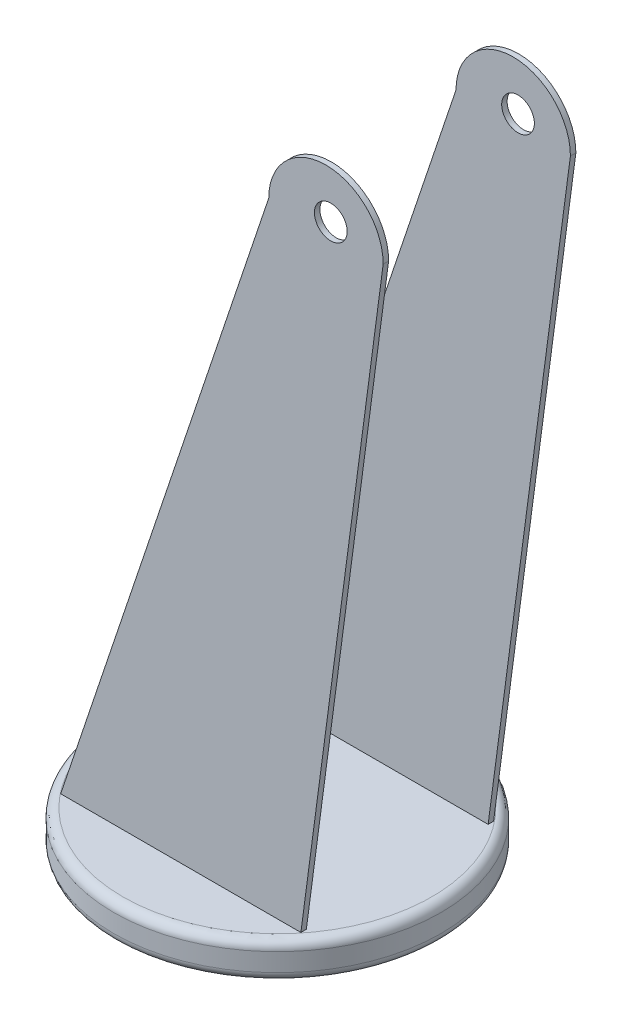
SolidWorks part; units mm, degrees
ref_plane "Front Plane" through (0, 0, 0) normal (0, 0, 1) x (1, 0, 0)
ref_plane "Top Plane" through (0, 0, 0) normal (0, 1, 0) x (1, 0, 0)
ref_plane "Right Plane" through (0, 0, 0) normal (1, 0, 0) x (0, 0, -1)
sketch "Sketch1" plane through (0, 0, 0) normal (0, 1, 0) x (1, 0, 0)
  circle A0 centre (0, 0) radius 9
  dimension "D1" = 18
extrude "Boss-Extrude1" add sketch "Sketch1" along normal blind 2
fillet "Fillet1" radius 0.5 2 edges at (0, 0, 9) (0, 2, 9)
ref_plane "Plane1" through (0, 0, 5) normal (0, 0, 1) x (1, 0, 0)
sketch "Sketch11" plane through (0, 0, 5) normal (0, 0, 1) x (1, 0, 0)
  line L1 (6.5499, 1.6691) -> (11.1208, 36.1053)
  line L2 (6.5499, 1.6691) -> (-6.7316, 1.6691)
  line L4 (-6.7316, 1.6691) -> (4.8267, 36.1053)
  circle A1 centre (8.2389, 36.6691) radius 0.9
  arc A2 (4.8267, 36.1053) -> (11.1208, 36.1053) centre (7.9737, 36.1053) cw
  dimension "D2" = 1.8
  dimension "D1" = 35
extrude "Boss-Extrude5" add sketch "Sketch11" along normal blind 0.3
mirror "Mirror1" about plane through (0, 0, 0) normal (0, 0, 1) of "Boss-Extrude5"
sketch "Sketch14" plane through (0, 0, 0) normal (0, -1, 0) x (1, 0, 0)
  circle A0 centre (0, 0) radius 1
  dimension "D1" = 2
extrude "Cut-Extrude1" cut sketch "Sketch14" against normal through all
